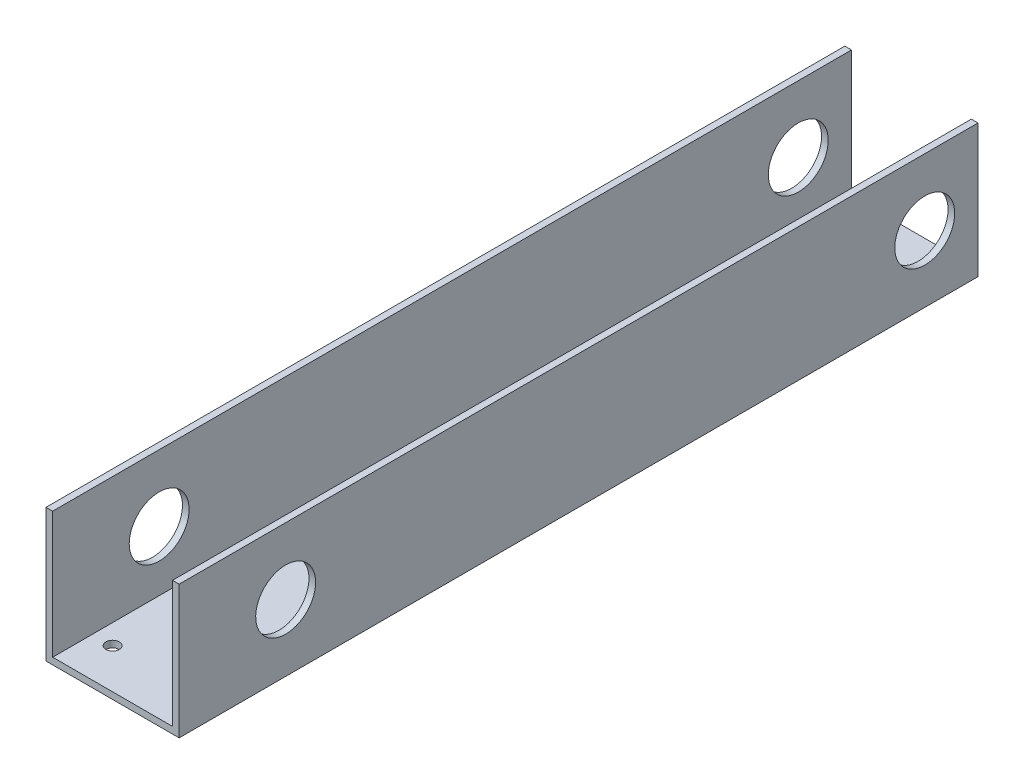
SolidWorks part; units mm, degrees
ref_plane "Front Plane" through (0, 0, 0) normal (0, 0, 1) x (1, 0, 0)
ref_plane "Top Plane" through (0, 0, 0) normal (0, 1, 0) x (1, 0, 0)
ref_plane "Right Plane" through (0, 0, 0) normal (1, 0, 0) x (0, 0, -1)
sketch "Sketch1" plane through (0, 0, 0) normal (0, 0, 1) x (1, 0, 0)
  line L0 (0, 0) -> (63.5, 0)
  line L1 (0, 0) -> (0, 63.5)
  line L2 (0, 63.5) -> (3.175, 63.5)
  line L3 (3.175, 63.5) -> (3.175, 3.175)
  line L4 (3.175, 3.175) -> (60.325, 3.175)
  line L5 (60.325, 3.175) -> (60.325, 63.5)
  line L6 (60.325, 63.5) -> (63.5, 63.5)
  line L7 (63.5, 63.5) -> (63.5, 0)
  dimension "D1" = 63.5
  dimension "D2" = 63.5
  dimension "D3" = 3.175
  dimension "D4" = 3.175
extrude "Boss-Extrude1" add sketch "Sketch1" along normal blind 381
sketch "Sketch2" plane through (0, 0, 0) normal (0, -1, 0) x (1, 0, 0)
  line L0 (12.7, 361.95) -> (12.7, 57.15) construction
  line L1 (12.7, 361.95) -> (50.8, 361.95) construction
  line L2 (50.8, 361.95) -> (50.8, 285.75) construction
  line L3 (50.8, 285.75) -> (12.7, 285.75) construction
  line L4 (50.8, 285.75) -> (50.8, 209.55) construction
  line L5 (50.8, 209.55) -> (12.7, 209.55) construction
  line L6 (50.8, 209.55) -> (50.8, 133.35) construction
  line L7 (50.8, 133.35) -> (12.7, 133.35) construction
  line L8 (50.8, 133.35) -> (50.8, 57.15) construction
  line L9 (50.8, 57.15) -> (12.7, 57.15) construction
  line L10 (0, 381) -> (63.5, 381) construction
  line L11 (0, 381) -> (0, 0) construction
  line L12 (63.5, 381) -> (63.5, 0) construction
  circle A0 centre (12.7, 361.95) radius 3.175
  circle A1 centre (50.8, 361.95) radius 3.175
  circle A2 centre (50.8, 285.75) radius 3.175
  circle A3 centre (12.7, 285.75) radius 3.175 construction
  circle A4 centre (12.7, 209.55) radius 3.175 construction
  circle A5 centre (50.8, 209.55) radius 3.175
  circle A6 centre (12.7, 133.35) radius 3.175 construction
  circle A7 centre (50.8, 133.35) radius 3.175
  circle A8 centre (12.7, 57.15) radius 3.175 construction
  circle A9 centre (50.8, 57.15) radius 3.175
  dimension "D5" = 6.35
  dimension "D1" = 19.05
  dimension "D2" = 12.7
  dimension "D3" = 12.7
  dimension "D4" = 76.2
extrude "Cut-Extrude1" cut sketch "Sketch2" against normal through all both and the other way through all
sketch "Sketch3" plane through (63.5, 0, 0) normal (1, 0, 0) x (0, 0, -1)
  line L0 (-25.4, 31.75) -> (-330.2, 31.75) construction
  line L1 (-381, 0) -> (0, 0) construction
  line L2 (-381, 0) -> (-381, 63.5) construction
  line L3 (0, 63.5) -> (0, 0) construction
  circle A0 centre (-25.4, 31.75) radius 14.2875
  circle A1 centre (-330.2, 31.75) radius 14.2875
  dimension "D1" = 28.575
  dimension "D2" = 31.75
  dimension "D3" = 50.8
  dimension "D4" = 25.4
extrude "Cut-Extrude2" cut sketch "Sketch3" against normal through all both and the other way through all
